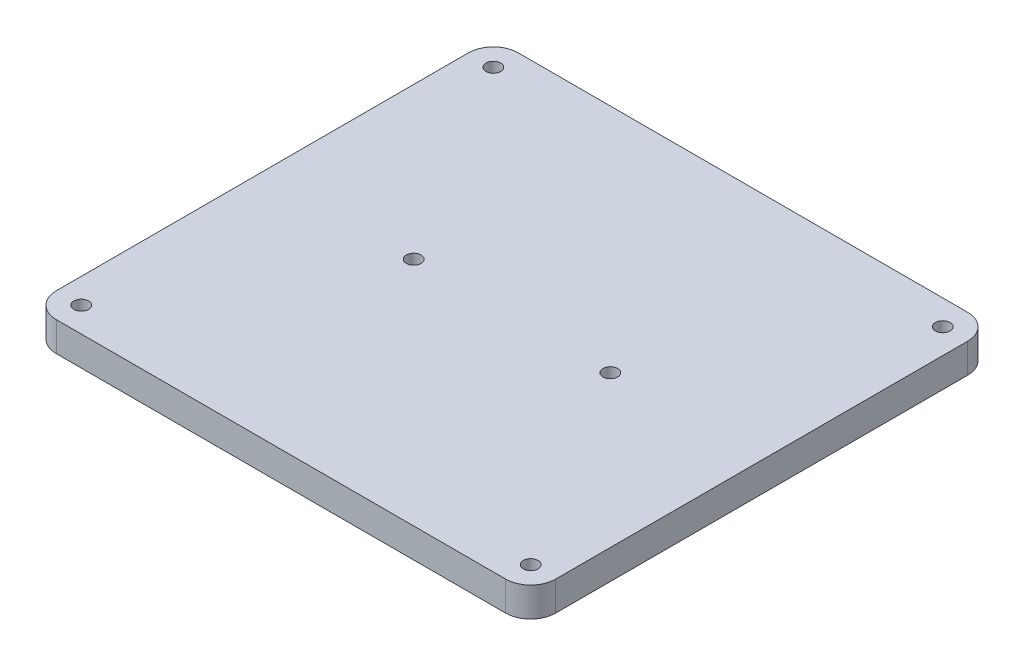
SolidWorks part; units mm, degrees
ref_plane "Front Plane" through (0, 0, 0) normal (0, 0, 1) x (1, 0, 0)
ref_plane "Top Plane" through (0, 0, 0) normal (0, 1, 0) x (1, 0, 0)
ref_plane "Right Plane" through (0, 0, 0) normal (1, 0, 0) x (0, 0, -1)
sketch "Sketch1" plane through (0, 0, 0) normal (0, 1, 0) x (1, 0, 0)
  line L0 (-25.4, 0) -> (25.4, 0) construction
  line L1 (-25.4, -23.5) -> (25.4, -23.5)
  line L2 (-25.4, -23.5) -> (-25.4, 23.5)
  line L3 (-25.4, 23.5) -> (25.4, 23.5)
  line L4 (25.4, -23.5) -> (25.4, 23.5)
  line L5 (0, 23.5) -> (0, -23.5) construction
  line L6 (-22.86, 23.5) -> (-22.86, 0) construction
  line L7 (-10, 0) -> (10, 0) construction
  circle A0 centre (-22.86, 20.96) radius 0.75
  circle A3 centre (22.86, 20.96) radius 0.75
  circle A5 centre (22.86, -20.96) radius 0.75
  circle A6 centre (-22.86, -20.96) radius 0.75
  circle A8 centre (10, 0) radius 0.75
  circle A9 centre (-10, 0) radius 0.75
  point P18 (0, 0)
  point P26 (0, 0)
  dimension "D3" = 1.5
  dimension "D1" = 47
  dimension "D2" = 50.8
  dimension "D4" = 2.54
  dimension "D5" = 2.54
  dimension "D6" = 20
extrude "Boss-Extrude1" add sketch "Sketch1" along normal blind 3
fillet "Fillet1" radius 2.54 4 edges at (-25.4, 1.5, -23.5) (25.4, 1.5, -23.5) (25.4, 1.5, 23.5) (-25.4, 1.5, 23.5)
